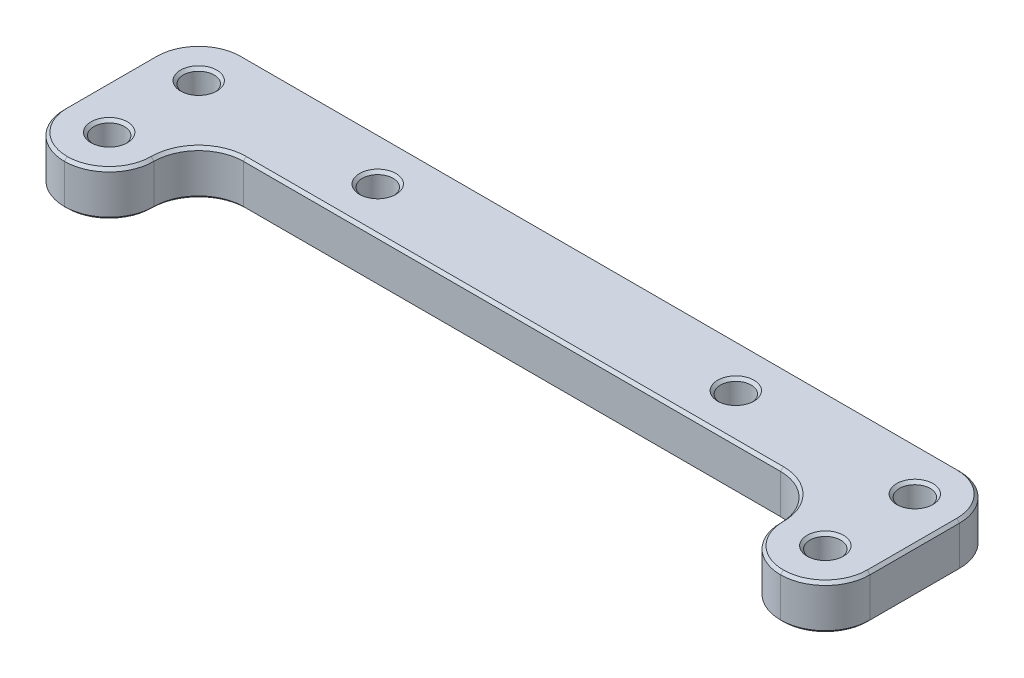
SolidWorks part; units mm, degrees
ref_plane "Front Plane" through (0, 0, 0) normal (0, 0, 1) x (1, 0, 0)
ref_plane "Top Plane" through (0, 0, 0) normal (0, 1, 0) x (1, 0, 0)
ref_plane "Right Plane" through (0, 0, 0) normal (1, 0, 0) x (0, 0, -1)
sketch "Sketch1" plane through (0, 0, 0) normal (0, 1, 0) x (1, 0, 0)
  line L0 (-101.6003, 6.35) -> (0.0003, 6.35)
  line L1 (6.35, 0.0003) -> (6.35, -12.7003)
  line L2 (0.0003, -19.05) -> (-0.0003, -19.05)
  line L3 (-6.35, -12.7003) -> (-6.35, -12.6997)
  line L4 (-12.6997, -6.35) -> (-88.9003, -6.35)
  line L5 (-95.25, -12.6997) -> (-95.25, -12.7003)
  line L6 (-101.5997, -19.05) -> (-101.6003, -19.05)
  line L7 (-107.95, -12.7003) -> (-107.95, 0.0003)
  circle A0 centre (0, 0) radius 2.1828
  circle A1 centre (-25.4, 0) radius 2.1828
  circle A2 centre (-76.2, 0) radius 2.1828
  circle A3 centre (-101.6, 0) radius 2.1828
  circle A4 centre (-101.6, -12.7) radius 2.1828
  circle A5 centre (0, -12.7) radius 2.1828
  arc A6 (-6.35, -12.6997) -> (-12.6997, -6.35) centre (-12.6997, -12.6997) ccw
  arc A7 (-0.0003, -19.05) -> (-6.35, -12.7003) centre (-0.0003, -12.7003) cw
  arc A8 (6.35, -12.7003) -> (0.0003, -19.05) centre (0.0003, -12.7003) cw
  arc A9 (0.0003, 6.35) -> (6.35, 0.0003) centre (0.0003, 0.0003) cw
  arc A10 (-101.6003, 6.35) -> (-107.95, 0.0003) centre (-101.6003, 0.0003) ccw
  arc A11 (-88.9003, -6.35) -> (-95.25, -12.6997) centre (-88.9003, -12.6997) ccw
  arc A12 (-95.25, -12.7003) -> (-101.5997, -19.05) centre (-101.5997, -12.7003) cw
  arc A13 (-101.6003, -19.05) -> (-107.95, -12.7003) centre (-101.6003, -12.7003) cw
  point P20 (0, 0)
  point P22 (-91.1709, -8.2424)
  point P23 (-70.1444, -29.9417)
  point P24 (-96.2172, -19.05)
  point P25 (-93.8623, -5.2146)
  dimension "D4" = 12.7
  dimension "D6" = 4.3656
  dimension "D7" = 4.3656
  dimension "D8" = 4.3656
  dimension "D9" = 4.3656
  dimension "D10" = 4.3656
  dimension "D11" = 4.3656
  dimension "D15" = 6.35
  dimension "D20" = 6.3497
  dimension "D1" = 101.6
  dimension "D2" = 25.4
  dimension "D3" = 25.4
  dimension "D5" = 12.7
  dimension "D12" = 6.35
  dimension "D13" = 6.35
  dimension "D14" = 6.35
  dimension "D16" = 6.35
  dimension "D17" = 6.35
  dimension "D18" = 6.35
  dimension "D19" = 6.35
extrude "Boss-Extrude1" add sketch "Sketch1" along normal blind 6.35
chamfer "Chamfer1" distance 0.3969 angle 45 44 edges at (0, 0, 14.8828) (-101.6, 0, 14.8828) (-101.6, 0, 2.1828) (-76.2, 0, 2.1828) (-25.4, 0, 2.1828) (0, 0, 2.1828) (-6.35, 0, 12.7) (-4.4902, 0, 17.1902) (0, 0, 19.05) (4.4902, 0, 17.1902) (6.35, 0, 6.35) (4.4902, 0, -4.4902) (-50.8, 0, -6.35) (-106.0902, 0, -4.4902) (-107.95, 0, 6.35) (-106.0902, 0, 17.1902) (-101.6, 0, 19.05) (-97.1098, 0, 17.1902) (-95.25, 0, 12.7) (-93.3902, 0, 8.2098) (-50.8, 0, 6.35) (-8.2098, 0, 8.2098) (0, 6.35, 14.8828) (-101.6, 6.35, 2.1828) (-25.4, 6.35, 2.1828) (-50.8, 6.35, 6.35) (-93.3902, 6.35, 8.2098) (-95.25, 6.35, 12.7) (-97.1098, 6.35, 17.1902) (-101.6, 6.35, 19.05) (-106.0902, 6.35, 17.1902) (-107.95, 6.35, 6.35) (-106.0902, 6.35, -4.4902) (-50.8, 6.35, -6.35) (4.4902, 6.35, -4.4902) (6.35, 6.35, 6.35) (4.4902, 6.35, 17.1902) (0, 6.35, 19.05) (-4.4902, 6.35, 17.1902) (-6.35, 6.35, 12.7) (-8.2098, 6.35, 8.2098) (0, 6.35, 2.1828) (-76.2, 6.35, 2.1828) (-101.6, 6.35, 14.8828)
